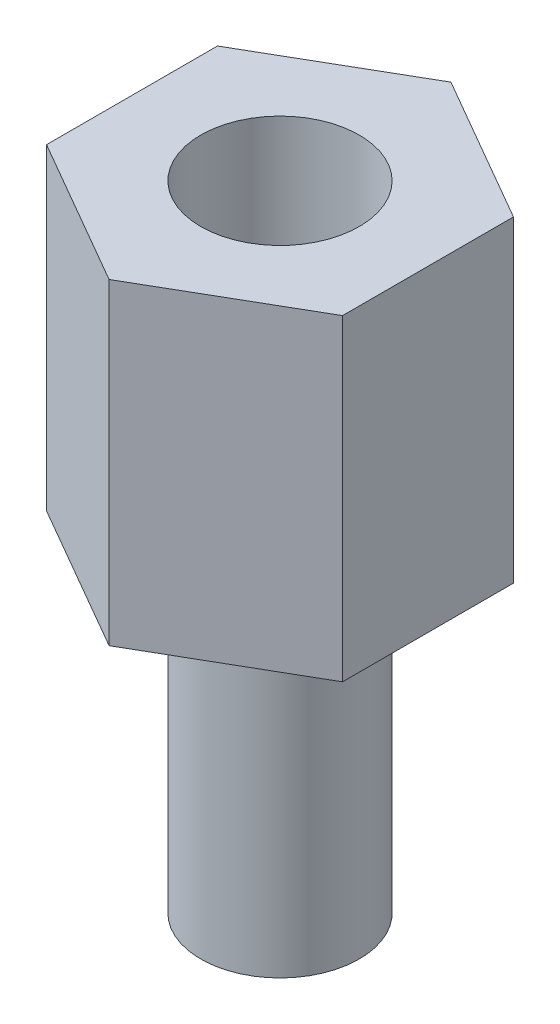
SolidWorks part; units mm, degrees
ref_plane "Front Plane" through (0, 0, 0) normal (0, 0, 1) x (1, 0, 0)
ref_plane "Top Plane" through (0, 0, 0) normal (0, 1, 0) x (1, 0, 0)
ref_plane "Right Plane" through (0, 0, 0) normal (1, 0, 0) x (0, 0, -1)
sketch "Sketch1" plane through (0, 0, 0) normal (0, 1, 0) x (1, 0, 0)
  line L1 (0, -3.2332) -> (2.8, -1.6166)
  line L2 (2.8, -1.6166) -> (2.8, 1.6166)
  line L3 (2.8, 1.6166) -> (0, 3.2332)
  line L4 (0, 3.2332) -> (-2.8, 1.6166)
  line L5 (-2.8, 1.6166) -> (-2.8, -1.6166)
  line L6 (-2.8, -1.6166) -> (0, -3.2332)
  circle A0 centre (0, 0) radius 2.8 construction
  dimension "D1" = 5.6
extrude "Boss-Extrude1" add sketch "Sketch1" along normal blind 6
sketch "Sketch2" plane through (0, 0, 0) normal (0, -1, 0) x (-1, 0, 0)
  circle A0 centre (0, 0) radius 1.5
  dimension "D1" = 3
extrude "Boss-Extrude2" add sketch "Sketch2" along normal blind 6
sketch "Sketch3" plane through (0, 6, 0) normal (0, 1, 0) x (1, 0, 0)
  circle A0 centre (0, 0) radius 1.5
  dimension "D1" = 3
extrude "Cut-Extrude1" cut sketch "Sketch3" against normal blind 4
